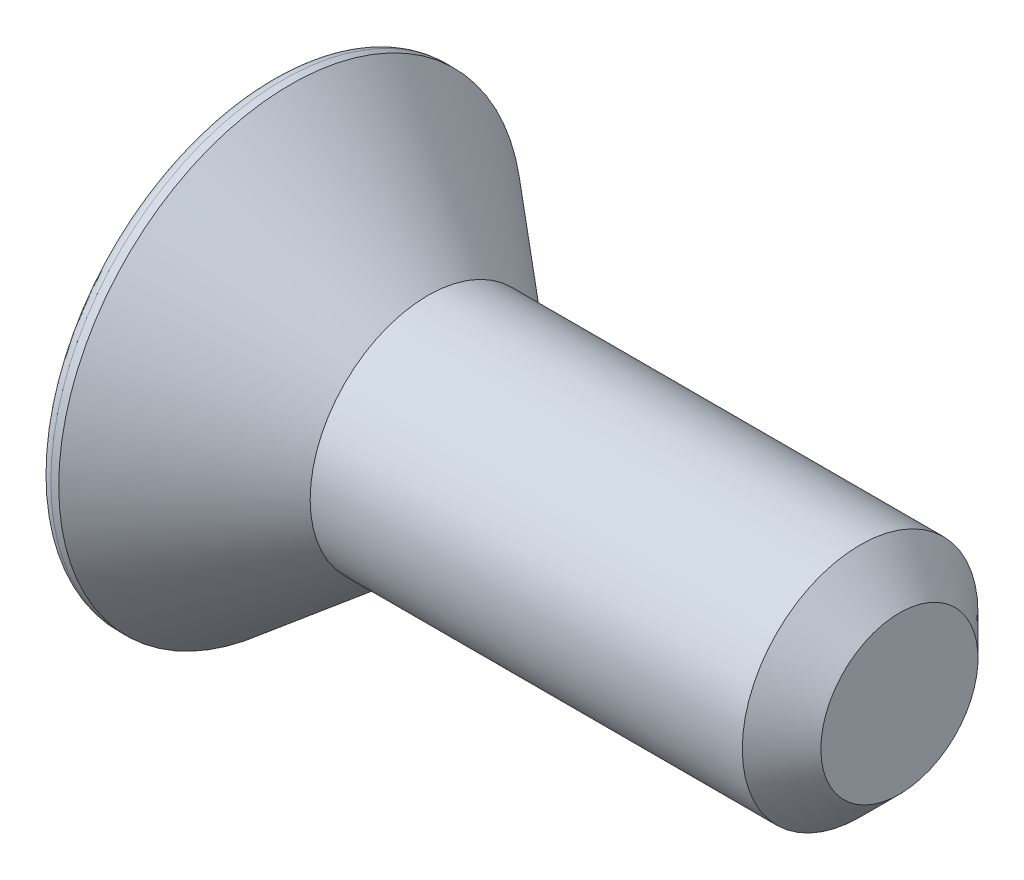
SolidWorks part; units mm, degrees
ref_plane "Спереди" through (0, 0, 0) normal (0, 0, 1) x (1, 0, 0)
ref_plane "Сверху" through (0, 0, 0) normal (0, 1, 0) x (1, 0, 0)
ref_plane "Справа" through (0, 0, 0) normal (1, 0, 0) x (0, 0, -1)
sketch "Эскиз1" plane through (0, 0, 0) normal (0, 0, 1) x (1, 0, 0)
  line L0 (0, 0) -> (0, 5.9)
  line L1 (0.5, 5.9) -> (4, 3)
  line L3 (4, 3) -> (16, 3)
  line L4 (16, 3) -> (16, 0)
  line L6 (0, 0) -> (16, 0)
  line L8 (0, 5.9) -> (0.5, 5.9)
  line L9 (0, 0) -> (-3.6011, 0) construction
  dimension "D4" = 0.5
  dimension "D1" = 4
  dimension "D2" = 11.8
  dimension "D3" = 6
  dimension "D5" = 16
revolve "Повернуть1" add sketch "Эскиз1" angle 360 about L6
cosmetic thread "Условное изображение резьбы1" parameters "D2"=4.891
sketch "Эскиз2" plane through (0, 0, 0) normal (-1, 0, 0) x (0, 0, 1)
  line L1 (1.1547, 2) -> (-1.1547, 2)
  line L2 (-1.1547, 2) -> (-2.3094, 0)
  line L3 (-2.3094, 0) -> (-1.1547, -2)
  line L4 (-1.1547, -2) -> (1.1547, -2)
  line L5 (1.1547, -2) -> (2.3094, 0)
  line L6 (2.3094, 0) -> (1.1547, 2)
  circle A0 centre (0, 0) radius 2 construction
  dimension "D1" = 4
extrude "Вырез-Вытянуть1" cut sketch "Эскиз2" against normal blind 3
fillet "Скругление1" radius 0.3 1 edges at (0, 0, 5.9)
chamfer "Фаска1" distance 1 angle 45 1 edges at (16, 0, 3)
